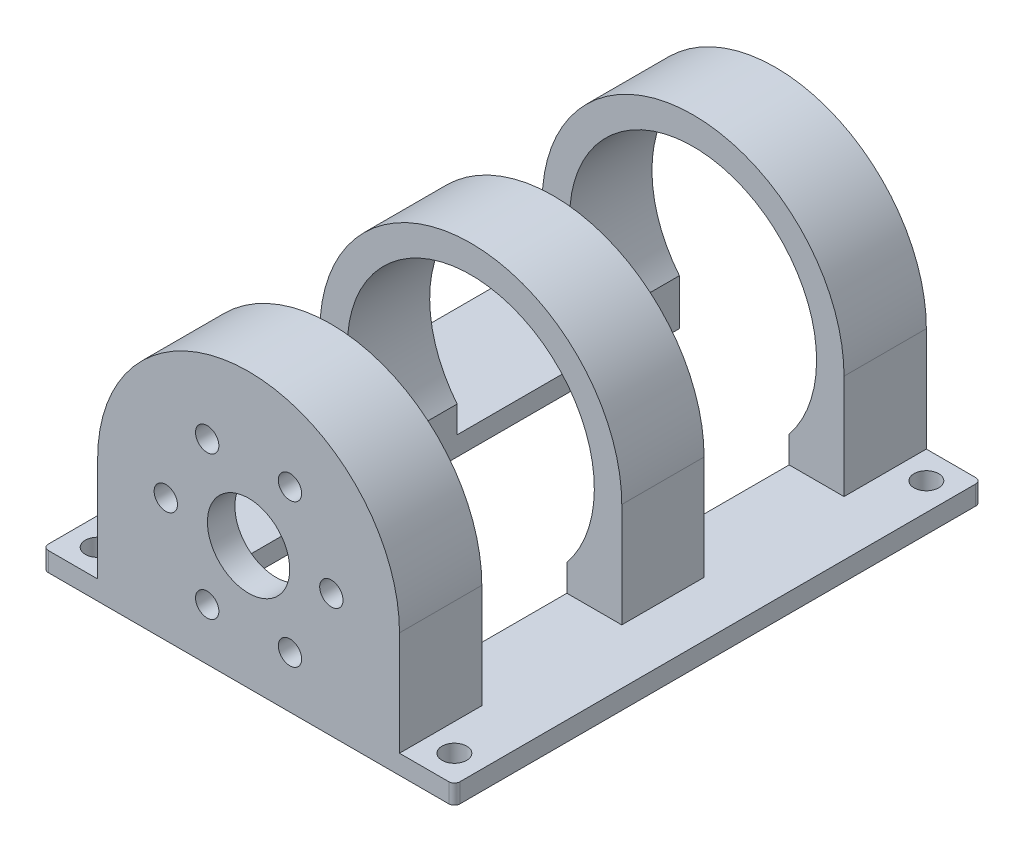
SolidWorks part; units mm, degrees
ref_plane "Front Plane" through (0, 0, 0) normal (0, 0, 1) x (1, 0, 0)
ref_plane "Top Plane" through (0, 0, 0) normal (0, 1, 0) x (1, 0, 0)
ref_plane "Right Plane" through (0, 0, 0) normal (1, 0, 0) x (0, 0, -1)
sketch "Sketch1" plane through (0, 0, 0) normal (0, 0, 1) x (1, 0, 0)
  line L10 (-27.5, -22.5) -> (-27.5, 0)
  line L12 (27.5, -22.5) -> (27.5, 0)
  line L13 (0, -22.5) -> (0, 27.5) construction
  line L14 (-27.5, -22.5) -> (-17.5, -22.5)
  line L15 (-17.5, -22.5) -> (-17.5, -14.1421)
  line L16 (27.5, -22.5) -> (17.5, -22.5)
  line L17 (17.5, -22.5) -> (17.5, -14.1421)
  arc A1 (17.5, -14.1421) -> (-17.5, -14.1421) centre (0, 0) ccw
  arc A2 (27.5, 0) -> (-27.5, 0) centre (0, 0) ccw
  point P6 (0, 27.5)
  dimension "D1" = 22.5
  dimension "D6" = 27.5
  dimension "D2" = 50
  dimension "D4" = 10
extrude "Boss-Extrude2" add sketch "Sketch1" along normal blind 96
sketch "Sketch4" plane through (0, -22.5, 0) normal (0, -1, 0) x (1, 0, 0)
  line L0 (-27.5, 0) -> (-17.5, 0) construction
  line L1 (-27.5, 96) -> (-37.5, 96)
  line L2 (-27.5, 96) -> (-27.5, 0)
  line L3 (-27.5, 0) -> (-37.5, 0)
  line L4 (-37.5, 96) -> (-37.5, 0)
  line L5 (-37.5, 48) -> (27.5, 48) construction
  line L6 (27.5, 96) -> (27.5, 0) construction
  line L7 (0, 0) -> (0, 96) construction
  line L8 (-22.5, 0) -> (22.5, 0) construction
  line L9 (22.5, 96) -> (-22.5, 96) construction
  line L10 (27.5, 0) -> (37.5, 0)
  line L11 (37.5, 96) -> (37.5, 0)
  line L12 (27.5, 96) -> (37.5, 96)
  line L13 (27.5, 96) -> (27.5, 0)
  circle A0 centre (-32.5, 91) radius 2.25
  circle A1 centre (-32.5, 5) radius 2.25
  circle A2 centre (32.5, 5) radius 2.25
  circle A3 centre (32.5, 91) radius 2.25
  dimension "D1" = 4.5
  dimension "D2" = 5
  dimension "D3" = 5
  dimension "D4" = 10
extrude "Boss-Extrude3" add sketch "Sketch4" against normal blind 3.5
sketch "Sketch5" plane through (0, 0, 96) normal (0, 0, 1) x (1, 0, 0)
  line L1 (-37.5, -22.5) -> (-17.5, -22.5) construction
  line L18 (-27.5, -19) -> (-27.5, 0)
  line L25 (27.5, -19) -> (27.5, 0)
  line L26 (-27.5, -19) -> (-27.5, -22.5)
  line L27 (27.5, -19) -> (27.5, -22.5)
  line L28 (-27.5, -22.5) -> (27.5, -22.5)
  arc A0 (27.5, 0) -> (-27.5, 0) centre (0, 0) ccw
  arc A1 (27.5, 0) -> (-27.5, 0) centre (0, 0) ccw construction
extrude "Boss-Extrude4" add sketch "Sketch5" along normal blind 5 from offset 5 offset against normal yes
sketch "Sketch6" plane through (0, 0, 96) normal (0, 0, 1) x (1, 0, 0)
  circle A0 centre (0, 0) radius 22.5 construction
  arc A2 (17.5, -14.1421) -> (-17.5, -14.1421) centre (0, 0) ccw construction
  circle A3 centre (0, 0) radius 15.0833 construction
  circle A4 centre (-7.5417, 13.0625) radius 2.125
  circle A5 centre (7.5417, 13.0625) radius 2.125
  circle A6 centre (15.0833, 0) radius 2.125
  circle A7 centre (7.5417, -13.0625) radius 2.125
  circle A8 centre (-7.5417, -13.0625) radius 2.125
  circle A9 centre (-15.0833, 0) radius 2.125
  point P26 (0, 0)
  dimension "D1" = 5.2917
  dimension "D2" = 2.125
  dimension "D4" = 15.0833
  dimension "D5" = 15.0833
  dimension "D3" = 6
extrude "Cut-Extrude1" cut sketch "Sketch6" against normal blind 5
sketch "Sketch7" plane through (0, 0, 96) normal (0, 0, 1) x (1, 0, 0)
  circle A0 centre (0, 0) radius 7.5
  dimension "D1" = 15
extrude "Cut-Extrude2" cut sketch "Sketch7" against normal through all
sketch "Sketch8" plane through (0, -19, 0) normal (0, 1, 0) x (1, 0, 0)
  line L0 (-27.5, 0) -> (-27.5, -96) construction
  line L1 (-27.5, -15) -> (27.5, -15)
  line L2 (-27.5, -15) -> (-27.5, -40.5)
  line L3 (-27.5, -40.5) -> (27.5, -40.5)
  line L4 (27.5, -15) -> (27.5, -40.5)
  line L5 (27.5, -96) -> (27.5, 0) construction
  line L6 (-27.5, -96) -> (27.5, -96) construction
  line L7 (-27.5, -55.5) -> (27.5, -55.5)
  line L8 (-27.5, -55.5) -> (-27.5, -81)
  line L9 (-27.5, -81) -> (27.5, -81)
  line L10 (27.5, -55.5) -> (27.5, -81)
  line L11 (27.5, 0) -> (-27.5, 0) construction
  dimension "D1" = 15
  dimension "D2" = 15
  dimension "D3" = 15
extrude "Cut-Extrude3" cut sketch "Sketch8" along normal through all
fillet "Fillet1" radius 1 4 edges at (-37.5, -20.75, 0) (37.5, -20.75, 0) (-37.5, -20.75, 96) (37.5, -20.75, 96)
